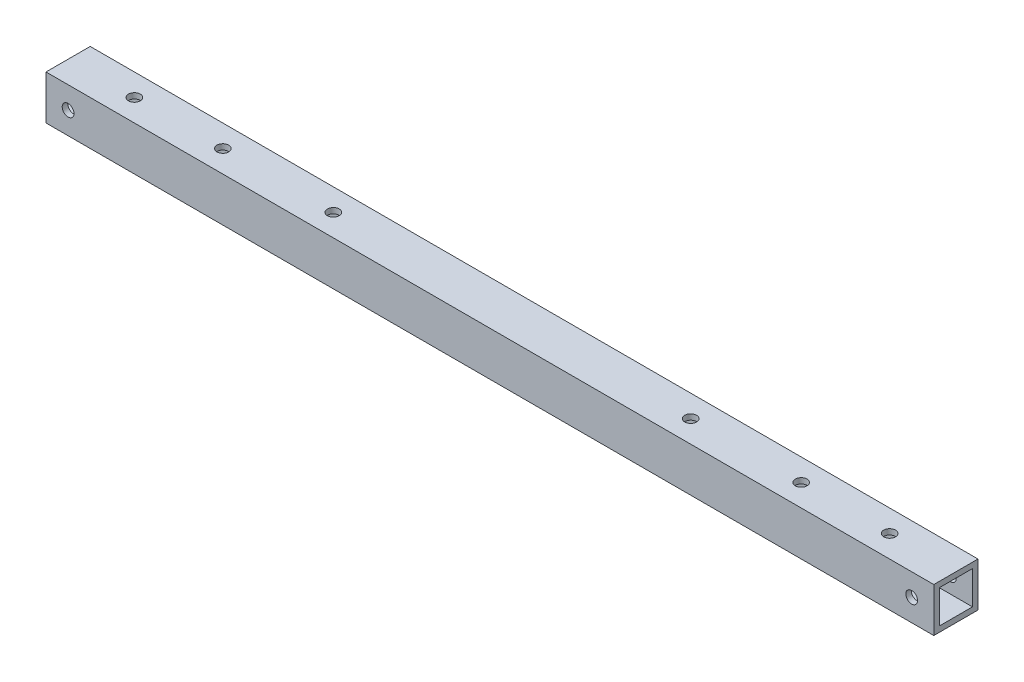
SolidWorks part; units mm, degrees
ref_plane "正面" through (0, 0, 0) normal (0, 0, 1) x (1, 0, 0)
ref_plane "平面" through (0, 0, 0) normal (0, 1, 0) x (1, 0, 0)
ref_plane "右側面" through (0, 0, 0) normal (1, 0, 0) x (0, 0, -1)
sketch "ｽｹｯﾁ1" plane through (0, 0, 0) normal (1, 0, 0) x (0, 0, -1)
  line L0 (1.5, 10.5) -> (10.5, 10.5)
  line L1 (0, 12) -> (12, 12)
  line L2 (0, 12) -> (0, 0)
  line L3 (0, 0) -> (12, 0)
  line L4 (12, 12) -> (12, 0)
  line L5 (0, 12) -> (12, 0) construction
  line L6 (0, 0) -> (12, 12) construction
  line L7 (10.5, 10.5) -> (10.5, 1.5)
  line L8 (1.5, 1.5) -> (10.5, 1.5)
  line L9 (1.5, 10.5) -> (1.5, 1.5)
  point P0 (6, 6)
  dimension "D1" = 12
  dimension "D2" = 12
  dimension "D3" = 1.5
extrude "ﾎﾞｽ - 押し出し1" add sketch "ｽｹｯﾁ1" along normal blind 241
sketch "ｽｹｯﾁ2" plane through (0, 12, 0) normal (0, 1, 0) x (1, 0, 0)
  line L0 (-126.8441, 6) -> (280.8054, 6) construction
  line L1 (0, 12) -> (0, 0) construction
  line L2 (241, 12) -> (241, 0) construction
  circle A0 centre (18, 6) radius 1.6
  circle A1 centre (223, 6) radius 1.6
  point P4 (0, 6)
  point P7 (241, 6)
  dimension "D1" = 3.2
  dimension "D3" = 18
  dimension "D2" = 18
extrude "ｶｯﾄ - 押し出し1" cut sketch "ｽｹｯﾁ2" against normal through all
sketch "ｽｹｯﾁ3" plane through (0, 0, 0) normal (0, 0, 1) x (1, 0, 0)
  line L0 (-20.0536, 6) -> (343.4105, 6) construction
  line L1 (0, 12) -> (0, 0) construction
  line L2 (241, 12) -> (241, 0) construction
  circle A0 centre (6, 6) radius 1.6
  circle A1 centre (235, 6) radius 1.6
  point P4 (0, 6)
  point P7 (241, 6)
  dimension "D1" = 3.2
  dimension "D2" = 6
  dimension "D3" = 6
extrude "ｶｯﾄ - 押し出し2" cut sketch "ｽｹｯﾁ3" against normal through all
sketch "ｽｹｯﾁ4" plane through (0, 0, 0) normal (0, -1, 0) x (1, 0, 0)
  line L0 (36, -6) -> (78, -6) construction
  line L1 (36, 0) -> (78, 0) construction
  line L2 (36, 0) -> (36, -12) construction
  line L3 (36, -12) -> (78, -12) construction
  line L4 (78, 0) -> (78, -12) construction
  line L5 (36, 0) -> (78, -12) construction
  line L6 (36, -12) -> (78, 0) construction
  line L11 (0, 0) -> (0, -12) construction
  line L12 (241, 0) -> (0, 0) construction
  line L13 (163, -6) -> (205, -6) construction
  line L14 (163, 0) -> (205, 0) construction
  line L15 (163, 0) -> (163, -12) construction
  line L16 (163, -12) -> (205, -12) construction
  line L17 (205, 0) -> (205, -12) construction
  line L18 (163, 0) -> (205, -12) construction
  line L19 (163, -12) -> (205, 0) construction
  line L20 (241, 0) -> (241, -12) construction
  circle A0 centre (42, -6) radius 1.6
  circle A1 centre (72, -6) radius 1.6
  circle A2 centre (169, -6) radius 1.6
  circle A3 centre (199, -6) radius 1.6
  point P0 (57, -6)
  point P8 (57, -6)
  point P18 (184, -6)
  point P26 (184, -6)
  dimension "D3" = 3.2
  dimension "D6" = 3.2
  dimension "D1" = 42
  dimension "D2" = 36
  dimension "D4" = 6
  dimension "D5" = 6
  dimension "D7" = 6
  dimension "D8" = 6
  dimension "D9" = 36
  dimension "D10" = 42
extrude "ｶｯﾄ - 押し出し3" cut sketch "ｽｹｯﾁ4" against normal through all
